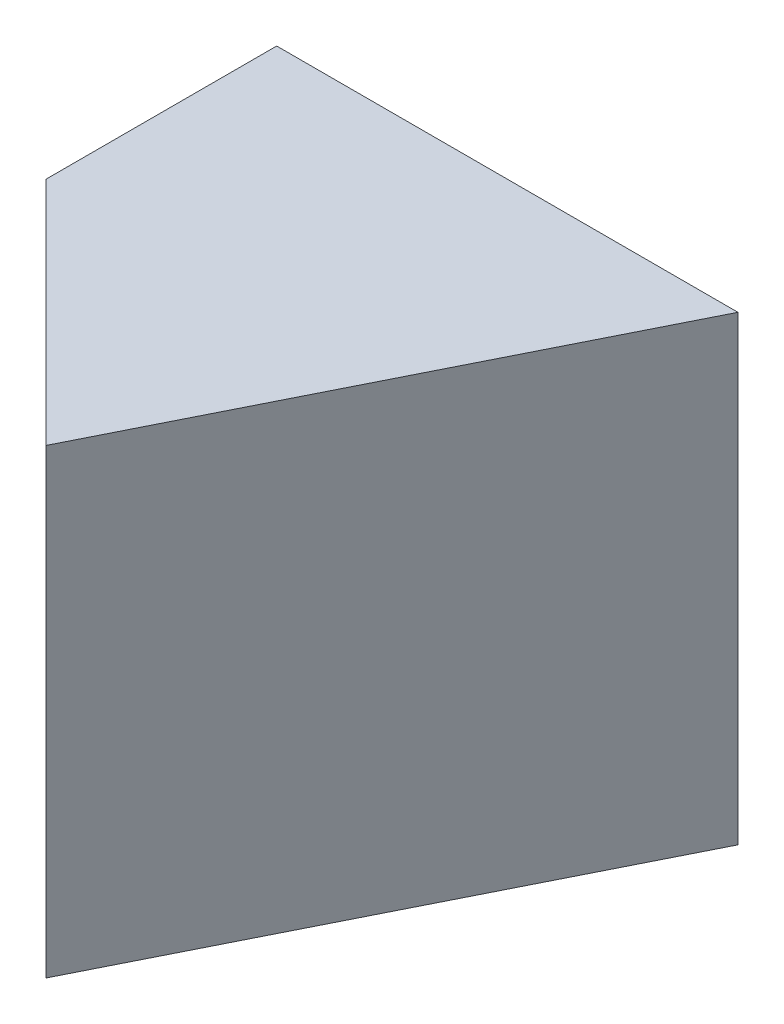
SolidWorks part; units mm, degrees
ref_plane "Front Plane" through (0, 0, 0) normal (0, 0, 1) x (1, 0, 0)
ref_plane "Top Plane" through (0, 0, 0) normal (0, 1, 0) x (1, 0, 0)
ref_plane "Right Plane" through (0, 0, 0) normal (1, 0, 0) x (0, 0, -1)
sketch "Sketch1" plane through (0, 0, 0) normal (0, 0, 1) x (1, 0, 0)
  line L1 (0, 0) -> (20, 0)
  line L2 (0, 0) -> (0, 20)
  line L3 (0, 20) -> (20, 20)
  line L4 (20, 0) -> (20, 20)
  dimension "D1" = 20
  dimension "D2" = 20
extrude "Boss-Extrude1" add sketch "Sketch1" along normal blind 20
sketch "Sketch2" plane through (0, 20, 0) normal (0, 1, 0) x (1, 0, 0)
  line L0 (20, 0) -> (10, -20)
  line L1 (20, -20) -> (0, -20) construction
  line L2 (10, -20) -> (20, -20)
  line L3 (20, -20) -> (20, 0)
extrude "Cut-Extrude1" cut sketch "Sketch2" against normal blind 20
sketch "Sketch3" plane through (0, 20, 0) normal (0, 1, 0) x (1, 0, 0)
  line L0 (0, -20) -> (10, -20)
  line L1 (10, -20) -> (0, -10)
  line L2 (0, -20) -> (0, 0) construction
  line L3 (0, -10) -> (0, -20)
extrude "Cut-Extrude2" cut sketch "Sketch3" against normal blind 20
